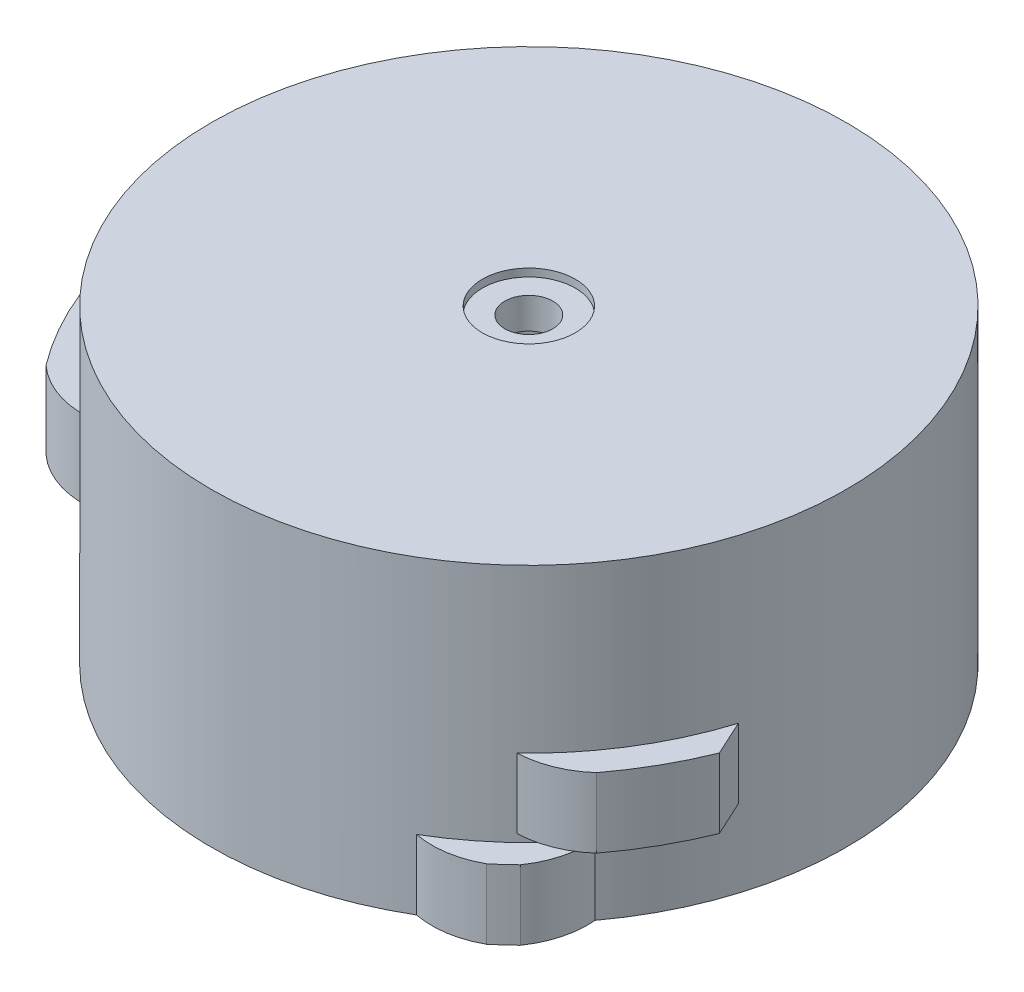
SolidWorks part; units mm, degrees
ref_plane "Front Plane" through (0, 0, 0) normal (0, 0, 1) x (1, 0, 0)
ref_plane "Top Plane" through (0, 0, 0) normal (0, 1, 0) x (1, 0, 0)
ref_plane "Right Plane" through (0, 0, 0) normal (1, 0, 0) x (0, 0, -1)
sketch "Sketch2" plane through (0, 0, 0) normal (0, 1, 0) x (1, 0, 0)
  circle A0 centre (0, 0) radius 41
  dimension "D1" = 82
extrude "Boss-Extrude1" add sketch "Sketch2" along normal blind 40
ref_plane "Plane1" through (0, 1, 0) normal (0, 1, 0) x (1, 0, 0)
sketch "Sketch3" plane through (0, 0, 0) normal (0, 1, 0) x (1, 0, 0)
  line L0 (0, 0) -> (0, -41) construction
  line L1 (0, 0) -> (15.7736, -17.5184) construction
  line L2 (0, 0) -> (28.604, -34.089) construction
  line L3 (0, 0) -> (30.9123, -32.0106) construction
  line L4 (28.604, -34.089) -> (25.8133, -35.1899) construction
  line L5 (25.8133, -35.1899) -> (20.8151, -35.3232) construction
  circle A0 centre (0, 0) radius 41 construction
  arc A5 (28.604, -34.089) -> (30.9123, -32.0106) centre (0, 0) ccw
  arc A6 (28.604, -34.089) -> (20.8151, -35.3232) centre (23.014, -24.0062) cw
  arc A7 (30.9123, -32.0106) -> (32.954, -24.3934) centre (21.469, -25.3973) ccw
  circle A10 centre (0, 0) radius 41
  arc A11 (20.8151, -35.3232) -> (32.954, -24.3934) centre (0, 0) ccw
  dimension "D4" = 3
  dimension "D5" = 5
  dimension "D7" = 0
  dimension "D1" = 44
  dimension "D2" = 44.5
  dimension "D3" = 2
  dimension "D6" = 160
extrude "Home" add sketch "Sketch3" along normal blind 9
ref_plane "Plane2" through (0, 10, 0) normal (0, 1, 0) x (1, 0, 0)
sketch "Sketch4" plane through (0, 10, 0) normal (0, 1, 0) x (1, 0, 0)
  line L0 (0, 0) -> (0, -41) construction
  line L2 (0, 0) -> (35.5393, -26.7808) construction
  line L3 (0, 0) -> (41.2597, -16.67) construction
  line L4 (35.5393, -26.7808) -> (33.0677, -28.4812) construction
  line L5 (33.0677, -28.4812) -> (28.2276, -29.7355) construction
  line L6 (41.2597, -16.67) -> (39.1645, -12.1301)
  circle A0 centre (0, 0) radius 41 construction
  arc A2 (35.5393, -26.7808) -> (28.2276, -29.7355) centre (27.8244, -18.2138) cw
  arc A5 (41.2597, -16.67) -> (35.5393, -26.7808) centre (0, 0) cw
  arc A7 (20.8151, -35.3232) -> (32.954, -24.3934) centre (0, 0) ccw construction
  circle A9 centre (0, 0) radius 41
  arc A10 (28.2276, -29.7355) -> (39.1645, -12.1301) centre (0, 0) ccw
  dimension "D1" = 53
  dimension "D2" = 44.5
  dimension "D3" = 15
  dimension "D4" = 160
  dimension "D5" = 3
  dimension "D6" = 5
  dimension "D7" = 0
  dimension "D8" = 5
extrude "End R" add sketch "Sketch4" along normal blind 9
sketch "Sketch6" plane through (0, 19, 0) normal (0, 1, 0) x (1, 0, 0)
  line L0 (0, 0) -> (0, -41) construction
  line L1 (0, 0) -> (-35.5393, -26.7808) construction
  line L2 (0, 0) -> (-41.2597, -16.67) construction
  line L3 (-35.5393, -26.7808) -> (-33.0877, -28.5098) construction
  line L4 (-33.0877, -28.5098) -> (-28.0877, -29.8678) construction
  line L5 (-41.2597, -16.67) -> (-39.3041, -11.67)
  circle A0 centre (0, 0) radius 41 construction
  arc A1 (-35.5393, -26.7808) -> (-28.0877, -29.8678) centre (-27.5728, -18.0877) ccw
  arc A2 (-35.5393, -26.7808) -> (-41.2597, -16.67) centre (0, 0) cw
  circle A4 centre (0, 0) radius 41
  arc A6 (-39.3041, -11.67) -> (-28.0877, -29.8678) centre (0, 0) ccw
  dimension "D1" = 53
  dimension "D2" = 44.5
  dimension "D3" = 15
  dimension "D4" = 160
  dimension "D5" = 3
  dimension "D6" = 5
  dimension "D7" = 5
  dimension "D8" = 0
extrude "End L" add sketch "Sketch6" along normal blind 10
sketch "Sketch8" plane through (0, 0, 0) normal (0, -1, 0) x (1, 0, 0)
  circle A0 centre (0, 0) radius 35
  dimension "D1" = 70
extrude "Cut-Extrude1" cut sketch "Sketch8" against normal blind 10
sketch "Sketch10" plane through (0, 10, 0) normal (0, -1, 0) x (1, 0, 0)
  line L2 (0, -11.2596) -> (0, -8.2596) construction
  line L3 (-2.5, -8.2596) -> (2.5, -8.2596)
  line L4 (3, -8.7596) -> (3, -10.8426)
  line L5 (-3, -8.7596) -> (-3, -10.8426)
  arc A3 (3, -10.8426) -> (-3, -10.8426) centre (0, 0) ccw
  arc A4 (2.5, -8.2596) -> (3, -8.7596) centre (2.5, -8.7596) cw
  arc A5 (-2.5, -8.2596) -> (-3, -8.7596) centre (-2.5, -8.7596) ccw
  point P8 (0, -8.2596)
  point P11 (3, -8.2596)
  point P12 (-3, -8.2596)
  point P15 (-3, -8.2596)
  dimension "D1" = 22.5
  dimension "D5" = 0.5
  dimension "D2" = 3
  dimension "D3" = 6
  dimension "D4" = 2.583
extrude "Cut-Extrude3" cut sketch "Sketch10" against normal blind 25
sketch "Sketch11" plane through (0, 35, 0) normal (0, -1, 0) x (1, 0, 0)
  circle A0 centre (0, 0) radius 3.1
  dimension "D1" = 6.2
extrude "Cut-Extrude4" cut sketch "Sketch11" against normal up to next
sketch "Sketch12" plane through (0, 40, 0) normal (0, 1, 0) x (1, 0, 0)
  circle A0 centre (0, 0) radius 6
  dimension "D1" = 12
extrude "Cut-Extrude5" cut sketch "Sketch12" against normal blind 1
sketch "Sketch13" plane through (0, 0, 0) normal (0, -1, 0) x (1, 0, 0)
  circle A0 centre (0, 0) radius 41
  circle A1 centre (0, 0) radius 35
  circle A2 centre (0, 0) radius 41 construction
  dimension "D1" = 70
extrude "Boss-Extrude6" [suppressed] add sketch "Sketch13" along normal blind 6
